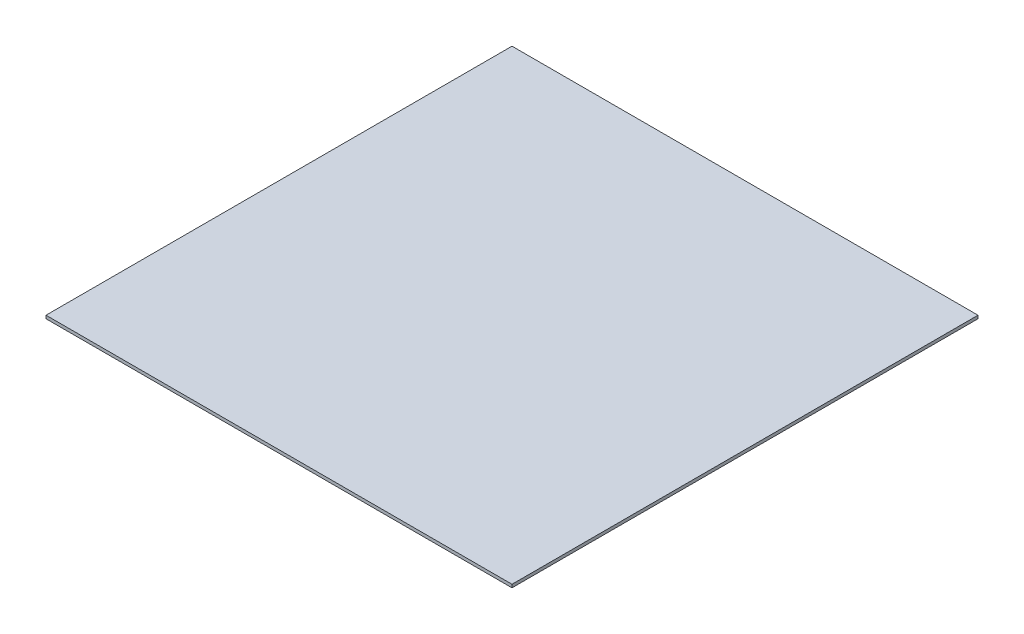
SolidWorks part; units mm, degrees
ref_plane "Front Plane" through (0, 0, 0) normal (0, 0, 1) x (1, 0, 0)
ref_plane "Top Plane" through (0, 0, 0) normal (0, 1, 0) x (1, 0, 0)
ref_plane "Right Plane" through (0, 0, 0) normal (1, 0, 0) x (0, 0, -1)
sketch "Sketch1" plane through (0, 92.4113, 0) normal (0, 1, 0) x (1, 0, 0)
  line L1 (82.4598, 318.3279) -> (232.4598, 318.3279)
  line L2 (82.4598, 318.3279) -> (82.4598, 168.3279)
  line L3 (82.4598, 168.3279) -> (232.4598, 168.3279)
  line L4 (232.4598, 318.3279) -> (232.4598, 168.3279)
extrude "Boss-Extrude1" add sketch "Sketch1" along normal blind 1
